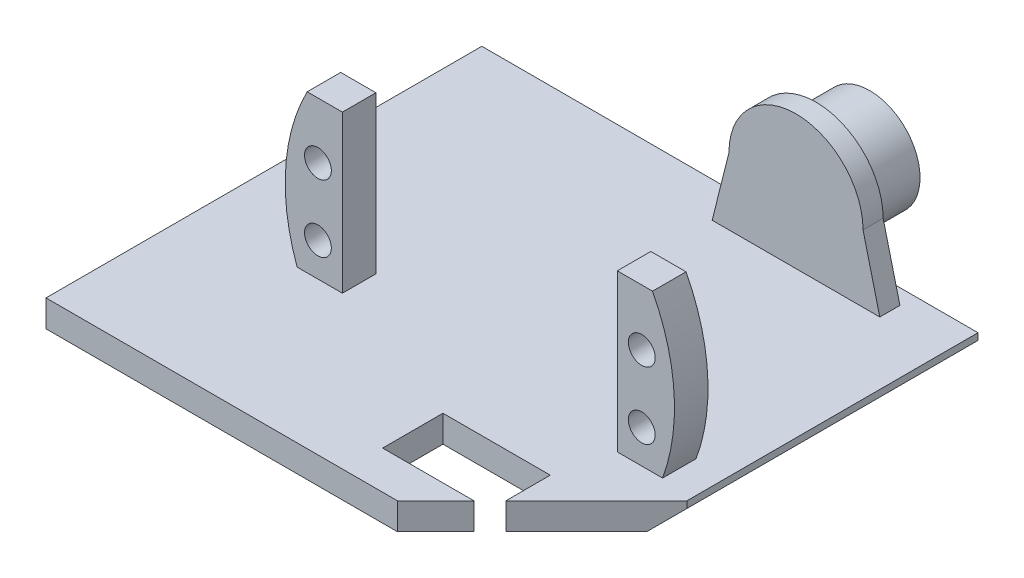
SolidWorks part; units mm, degrees
ref_plane "Alzado" through (0, 0, 0) normal (0, 0, 1) x (1, 0, 0)
ref_plane "Planta" through (0, 0, 0) normal (0, 1, 0) x (1, 0, 0)
ref_plane "Vista lateral" through (0, 0, 0) normal (1, 0, 0) x (0, 0, -1)
sketch "Croquis1" plane through (0, 0, 0) normal (0, 1, 0) x (1, 0, 0)
  line L0 (12.3319, -35.2047) -> (33.9208, -13.6159)
  line L1 (33.9208, 29.7953) -> (-40.0792, 29.7953)
  line L2 (33.9208, 29.7953) -> (33.9208, -13.6159)
  line L3 (12.3319, -35.2047) -> (-40.0792, -35.2047)
  line L4 (-40.0792, 29.7953) -> (-40.0792, -35.2047)
  line L5 (33.9208, 29.7953) -> (-40.0792, -35.2047) construction
  line L6 (32.3868, -24.0766) -> (-40.0792, 29.7953) construction
  point P0 (0, 0)
  dimension "D1" = 74
  dimension "D2" = 65
  dimension "D3" = 135
extrude "Saliente-Extruir1" add sketch "Croquis1" along normal blind 4
sketch "Croquis2" plane through (0, 4, 0) normal (0, 1, 0) x (1, 0, 0)
  line L0 (33.9208, 0) -> (-40.0792, 0) construction
  line L1 (33.9208, -13.6159) -> (33.9208, 29.7953) construction
  line L2 (-40.0792, -35.2047) -> (12.3319, -35.2047) construction
  line L3 (-40.0792, 29.7953) -> (-40.0792, -35.2047) construction
  line L4 (1.9208, -35.2047) -> (1.9208, 29.7953) construction
  line L5 (33.9208, 29.7953) -> (-40.0792, 29.7953) construction
  line L6 (29.1708, -12.5) -> (22.4208, -7.5) construction
  line L7 (-25.3292, -7.5) -> (-18.5792, -7.5)
  line L8 (-25.3292, -7.5) -> (-25.3292, -12.5)
  line L9 (-25.3292, -12.5) -> (-18.5792, -12.5)
  line L10 (-18.5792, -7.5) -> (-18.5792, -12.5)
  line L11 (-25.3292, -7.5) -> (-18.5792, -12.5) construction
  line L12 (-25.3292, -12.5) -> (-18.5792, -7.5) construction
  line L13 (29.1708, -7.5) -> (22.4208, -12.5) construction
  line L14 (22.4208, -7.5) -> (22.4208, -12.5)
  line L15 (29.1708, -12.5) -> (22.4208, -12.5)
  line L16 (29.1708, -7.5) -> (29.1708, -12.5)
  line L17 (29.1708, -7.5) -> (22.4208, -7.5)
  point P12 (-21.9542, -10)
  point P21 (25.7958, -10)
  point P23 (22.4208, -10)
  dimension "D1" = 41
  dimension "D2" = 32
  dimension "D3" = 10
  dimension "D4" = 54.5
  dimension "D5" = 5
  dimension "D6" = 41
extrude "Saliente-Extruir2" add sketch "Croquis2" along normal blind 18
sketch "Croquis3" plane through (0, 0, 12.5) normal (0, 0, 1) x (1, 0, 0)
  line L0 (-18.5792, 22) -> (-18.5792, 4) construction
  line L1 (-22.2292, 19) -> (-22.2292, 9) construction
  line L2 (-18.5792, 14.6783) -> (22.4208, 14.6783) construction
  line L3 (1.9208, 0) -> (1.9208, 25) construction
  line L4 (22.4208, 22) -> (22.4208, 4) construction
  line L5 (-25.3292, 4) -> (-18.5792, 4) construction
  circle A0 centre (-22.2292, 9) radius 2
  circle A1 centre (-22.2292, 19) radius 2
  circle A2 centre (26.0708, 19) radius 2
  circle A3 centre (26.0708, 9) radius 2
  point P4 (-22.2292, 14)
  point P29 (1.9208, 14.6783)
  dimension "D1" = 48.3
  dimension "D2" = 4
  dimension "D4" = 10
  dimension "D3" = 10
extrude "Cortar-Extruir1" cut sketch "Croquis3" against normal blind 10
sketch "Croquis5" plane through (0, 0, 12.5) normal (0, 0, 1) x (1, 0, 0)
  line L0 (-22.2292, 19) -> (-22.2292, 9) construction
  line L1 (-22.2292, 14) -> (26.0708, 14) construction
  line L2 (26.0708, 19) -> (26.0708, 9) construction
  line L3 (1.9208, 14) -> (1.9208, -2.6501) construction
  line L6 (-25.3292, 4) -> (-25.3292, 22)
  line L7 (-25.3292, 22) -> (-18.5792, 22)
  line L8 (-18.5792, 22) -> (-18.5792, 27.3934)
  line L9 (-18.5792, 27.3934) -> (-23.8315, 27.3934)
  line L10 (29.1708, 4) -> (29.1708, 22)
  line L11 (22.4208, 27.3934) -> (27.673, 27.3934)
  line L12 (22.4208, 22) -> (22.4208, 27.3934)
  line L13 (29.1708, 22) -> (22.4208, 22)
  arc A0 (-25.3292, 4) -> (-23.8315, 27.3934) centre (1.9208, 14) cw
  arc A1 (29.1708, 4) -> (27.673, 27.3934) centre (1.9208, 14) ccw
extrude "Saliente-Extruir3" add sketch "Croquis5" against normal up to surface (5 mm away) up to face at (-20.2292, 19, 7.5)
sketch "Croquis6" plane through (0, 4, 0) normal (0, 1, 0) x (1, 0, 0)
  line L0 (-18.5792, -7.5) -> (22.4208, -7.5) construction
  line L1 (22.4208, -7.5) -> (22.4208, 24.5) construction
  line L2 (22.4208, 24.5) -> (-18.5792, 24.5) construction
  line L3 (-18.5792, 24.5) -> (-18.5792, -7.5) construction
  line L4 (-0.4292, 24.5) -> (-0.4292, 27.5)
  line L5 (-0.4292, 27.5) -> (24.5708, 27.5)
  line L6 (24.5708, 27.5) -> (24.5708, 24.5)
  line L7 (24.5708, 24.5) -> (-0.4292, 24.5)
  line L8 (12.0708, 27.5) -> (12.0708, -15.294) construction
  dimension "D1" = 3
  dimension "D2" = 25
  dimension "D3" = 32
  dimension "D5" = 10.35
extrude "Saliente-Extruir4" add sketch "Croquis6" along normal blind 20
sketch "Croquis7" plane through (0, 0, -27.5) normal (0, 0, -1) x (-1, 0, 0)
  line L0 (-12.0708, 24) -> (-12.0708, 4) construction
  line L1 (-24.5708, 24) -> (0.4292, 24) construction
  line L2 (-24.5708, 4) -> (0.4292, 4) construction
  circle A0 centre (-12.0708, 14) radius 7.5
  dimension "D1" = 15
  dimension "D2" = 10
extrude "Saliente-Extruir5" add sketch "Croquis7" along normal blind 8
sketch "Croquis8" plane through (0, 0, -27.5) normal (0, 0, -1) x (-1, 0, 0)
  line L0 (-24.5708, 24) -> (0.4292, 24) construction
  line L1 (-24.5708, 4) -> (-22.0708, 14)
  line L2 (-2.0708, 14) -> (0.4292, 4)
  line L3 (0.4292, 4) -> (0.4292, 24)
  line L4 (0.4292, 24) -> (-24.5708, 24)
  line L5 (-24.5708, 24) -> (-24.5708, 4)
  arc A0 (-22.0708, 14) -> (-2.0708, 14) centre (-12.0708, 14) cw
  line M3 (0.4292, 4) -> (0.4292, 24)
  line M4 (0.4292, 24) -> (-24.5708, 24)
  line M5 (-24.5708, 24) -> (-24.5708, 4)
extrude "Cortar-Extruir2" cut sketch "Croquis8" against normal up to surface (3 mm away) contours L1 A0 L4 M5 | A0 L2 M4 M3 up to face at (12.0708, 14, -24.5)
sketch "Croquis9" plane through (0, 4, 0) normal (0, 1, 0) x (1, 0, 0)
  line L0 (20.4208, -25) -> (70.708, -25) construction
  line L1 (22.4208, -7.5) -> (12.4208, -7.5) construction
  line L2 (12.4208, -7.5) -> (12.4208, -25) construction
  line L3 (19.5708, 27.5) -> (70.708, 27.5) construction
  line L4 (20.4208, -20.5) -> (4.4208, -20.5)
  line L5 (20.4208, -20.5) -> (20.4208, -29.5)
  line L6 (20.4208, -29.5) -> (4.4208, -29.5)
  line L7 (4.4208, -20.5) -> (4.4208, -29.5)
  line L8 (20.4208, -20.5) -> (4.4208, -29.5) construction
  line L9 (20.4208, -29.5) -> (4.4208, -20.5) construction
  point P9 (4.4208, -25)
  point P10 (20.4208, -25)
  dimension "D1" = 52.5
  dimension "D2" = 10
  dimension "D3" = 13
  dimension "D4" = 9
  dimension "D5" = 16
extrude "Cortar-Extruir3" cut sketch "Croquis9" against normal up to next
chamfer "Chaflán1" distance 3 angle 45 1 edges at (33.9208, 0, -8.0897)
